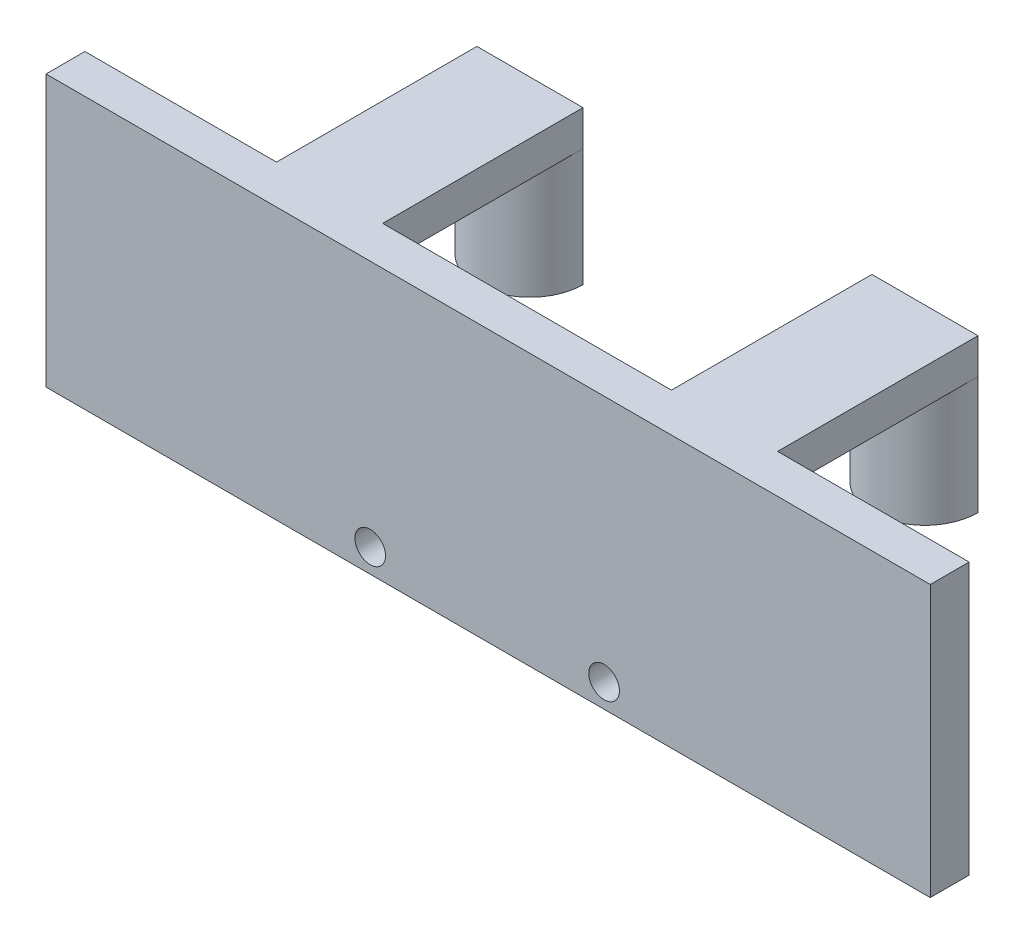
SolidWorks part; units mm, degrees
ref_plane "Спереди" through (0, 0, 0) normal (0, 0, 1) x (1, 0, 0)
ref_plane "Сверху" through (0, 0, 0) normal (0, 1, 0) x (1, 0, 0)
ref_plane "Справа" through (0, 0, 0) normal (1, 0, 0) x (0, 0, -1)
other "Configuration Table"
sketch "Эскиз1" plane through (0, 0, 0) normal (0, 1, 0) x (1, 0, 0)
  line L0 (0, 0) -> (-42.5, 0)
  line L1 (-42.5, 3.3) -> (-42.5, 20.3)
  line L2 (0, 3.3) -> (0, 20.3)
  line L3 (-42.5, 20.3) -> (-33.5, 20.3)
  line L4 (0, 20.3) -> (-9, 20.3)
  line L5 (-33.5, 20.3) -> (-33.5, 3.3)
  line L6 (-9, 20.3) -> (-9, 3.3)
  line L7 (-33.5, 3.3) -> (-9, 3.3)
  line L8 (-42.5, 0) -> (-58.75, 0)
  line L9 (0, 0) -> (16.25, 0)
  line L10 (0, 3.3) -> (16.25, 3.3)
  line L11 (-42.5, 3.3) -> (-58.75, 3.3)
  line L12 (-58.75, 3.3) -> (-58.75, 0)
  line L13 (16.25, 3.3) -> (16.25, 0)
  dimension "D1" = 42.5
  dimension "D2" = 9
  dimension "D3" = 9
  dimension "D4" = 20.3
  dimension "D5" = 17
  dimension "D6" = 20.3
extrude "Бобышка-Вытянуть1" add sketch "Эскиз1" along normal blind 23
sketch "Эскиз2" plane through (0, 0, 0) normal (0, -1, 0) x (1, 0, 0)
  line L0 (-42.5, -20.3) -> (-42.5, -3.3) construction
  line L1 (-9, -3.3) -> (-9, -20.3)
  line L2 (-33.5, -3.3) -> (-42.5, -3.3)
  line L3 (-9, -3.3) -> (0, -3.3)
  line L4 (0, -3.3) -> (0, -20.3) construction
  line L5 (0, -3.3) -> (0, -20.3)
  line L6 (0, -20.3) -> (-9, -20.3) construction
  line L7 (-42.5, -3.3) -> (-42.5, -20.3)
  line L9 (-33.5, -20.3) -> (-42.5, -20.3) construction
  line L12 (-33.5, -20.3) -> (-33.5, -3.3)
  line L13 (-9, -3.3) -> (-33.5, -3.3) construction
  line L14 (-33.5, -3.3) -> (-33.5, -20.3) construction
  arc A0 (-33.5, -20.3) -> (-42.5, -20.3) centre (-38, -20.3) ccw
  arc A1 (0, -20.3) -> (-9, -20.3) centre (-4.5, -20.3) ccw
extrude "Вырез-Вытянуть3" cut sketch "Эскиз2" against normal blind 20
sketch "Эскиз3" plane through (0, 0, 0) normal (0, 0, 1) x (1, 0, 0)
  line L1 (-58.75, 0) -> (16.25, 0) construction
  circle A0 centre (-31.25, 2) radius 1.3
  circle A1 centre (-11.414, 2) radius 1.3
  dimension "D1" = 2.6
  dimension "D2" = 2.6
  dimension "D3" = 2
  dimension "D4" = 2
extrude "Вырез-Вытянуть4" cut sketch "Эскиз3" against normal blind 4
sketch "Эскиз4" plane through (0, 0, 0) normal (0, -1, 0) x (1, 0, 0)
  line L0 (0, -20.3) -> (0, -3.3) construction
  line L1 (-42.5, -20.3) -> (0, -20.3)
  line L2 (-42.5, -20.3) -> (-42.5, -14.2974)
  line L3 (-42.5, -14.2974) -> (0, -14.2974)
  line L4 (0, -20.3) -> (0, -14.2974)
extrude "Вырез-Вытянуть5" cut sketch "Эскиз4" against normal blind 10
